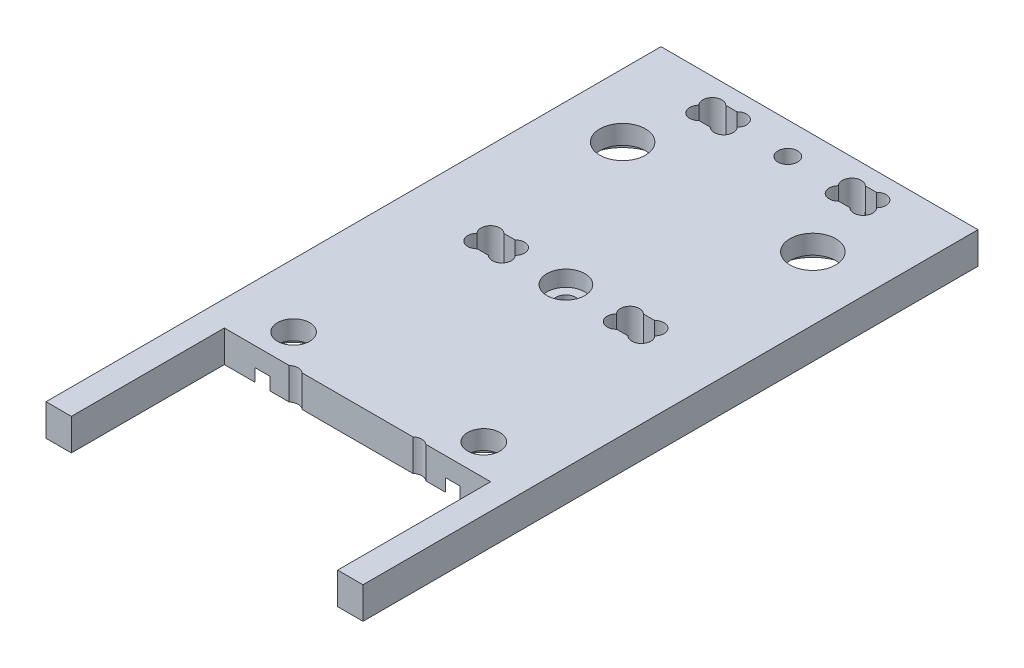
SolidWorks part; units mm, degrees
ref_plane "Alzado" through (0, 0, 0) normal (0, 0, 1) x (1, 0, 0)
ref_plane "Planta" through (0, 0, 0) normal (0, 1, 0) x (1, 0, 0)
ref_plane "Vista lateral" through (0, 0, 0) normal (1, 0, 0) x (0, 0, -1)
sketch "Croquis1" plane through (0, 0, 0) normal (0, 1, 0) x (1, 0, 0)
  line L0 (0, -36.0891) -> (0, 0) construction
  line L1 (-25, -48.5) -> (25, -48.5)
  line L2 (-25, -48.5) -> (-25, 48.5)
  line L3 (-25, 48.5) -> (25, 48.5)
  line L4 (25, -48.5) -> (25, 48.5)
  line L5 (-25, -48.5) -> (25, 48.5) construction
  line L6 (-25, 48.5) -> (25, -48.5) construction
  point P0 (0, 0)
  dimension "D2" = 50
  dimension "D1" = 97
extrude "Saliente-Extruir1" add sketch "Croquis1" along normal blind 5
sketch "Croquis3" plane through (0, 5, 0) normal (0, 1, 0) x (1, 0, 0)
  line L0 (0, -48.5) -> (0, 48.5) construction
  line L1 (-25, -48.5) -> (25, -48.5) construction
  line L2 (-14.1, -41.5) -> (-14.1, -48.5)
  line L3 (25, -48.5) -> (14.1, -48.5)
  line L4 (-25, -28.05) -> (-25, -48.5)
  line L5 (25, -28.05) -> (25, -48.5)
  line L6 (-25, -48.5) -> (-14.1, -48.5)
  line L7 (14.1, -41.5) -> (14.1, -48.5)
  line L10 (25, 48.5) -> (-25, 48.5) construction
  arc A0 (14.1, -41.5) -> (25, -28.05) centre (28.8286, -42.2945) cw
  arc A1 (-14.1, -41.5) -> (-25, -28.05) centre (-28.8286, -42.2945) ccw
  dimension "D1" = 7
  dimension "D3" = 29.5
  dimension "D2" = 20.45
  dimension "D4" = 14.1
extrude "Cortar-Extruir1" [suppressed] cut sketch "Croquis3" against normal through all
sketch "Croquis2" plane through (0, 5, 0) normal (0, 1, 0) x (1, 0, 0)
  line L0 (0, 6.5) -> (0, 48.5) construction
  line L1 (-15, -19.45) -> (15, -19.45) construction
  line L2 (-15, -19.45) -> (-15, 32.45) construction
  line L3 (-15, 32.45) -> (15, 32.45) construction
  line L4 (15, -19.45) -> (15, 32.45) construction
  line L5 (-15, -19.45) -> (15, 32.45) construction
  line L6 (-15, 32.45) -> (15, -19.45) construction
  line L7 (25, 48.5) -> (-25, 48.5) construction
  circle A0 centre (-15, 32.45) radius 3.6
  circle A1 centre (15, 32.45) radius 3.6
  circle A2 centre (15, -19.45) radius 2.55
  circle A3 centre (-15, -19.45) radius 2.55
  point P0 (0, 6.5)
  dimension "D3" = 7.2
  dimension "D5" = 5.1
  dimension "D1" = 30
  dimension "D2" = 51.9
  dimension "D4" = 42
extrude "Cortar-Extruir2" cut sketch "Croquis2" against normal through all
sketch "Croquis4" plane through (0, 0, 0) normal (0, -1, 0) x (1, 0, 0)
  circle A0 centre (15, -32.45) radius 6
  circle A1 centre (-15, -32.45) radius 6
  circle A2 centre (-15, 19.45) radius 5.05
  circle A3 centre (15, 19.45) radius 5.05
  dimension "D1" = 12
  dimension "D2" = 10.1
extrude "Cortar-Extruir3" cut sketch "Croquis4" against normal blind 2
fillet "Redondeo1" [suppressed] radius 5
sketch "Croquis5" plane through (0, 5, 0) normal (0, 1, 0) x (1, 0, 0)
  line L1 (-25, 45.6) -> (25, 45.6) construction
  line L2 (-25, 45.6) -> (-25, 41.4) construction
  line L3 (-25, 41.4) -> (25, 41.4) construction
  line L4 (25, 45.6) -> (25, 41.4) construction
  line L5 (-25, 48.5) -> (-25, -48.5) construction
  line L6 (25, -48.5) -> (25, 48.5) construction
  line L7 (25, 48.5) -> (-25, 48.5) construction
  line L8 (-11, 45.6) -> (-11, 41.4) construction
  line L9 (-14, 45.6) -> (-8, 45.6)
  line L10 (-14, 45.6) -> (-14, 41.4)
  line L11 (-14, 41.4) -> (-8, 41.4)
  line L12 (-8, 45.6) -> (-8, 41.4)
  line L13 (8, 45.6) -> (14, 45.6)
  line L14 (8, 45.6) -> (8, 41.4)
  line L15 (8, 41.4) -> (14, 41.4)
  line L16 (14, 45.6) -> (14, 41.4)
  line L17 (11, 45.6) -> (11, 41.4) construction
  line L18 (-11, 43.5) -> (-25, 43.5) construction
  line L19 (11, 43.5) -> (25, 43.5) construction
  line L20 (0, 45.6) -> (0, 41.4) construction
  circle A0 centre (0, 43.5) radius 1.55
  dimension "D5" = 3.1
  dimension "D1" = 4.2
  dimension "D2" = 2.9
  dimension "D3" = 6
  dimension "D4" = 14
extrude "Cortar-Extruir4" cut sketch "Croquis5" against normal through all
ref_plane "Plano1" through (0, 0, -43.5) normal (0, 0, 1) x (1, 0, 0)
ref_plane "Plano2" through (0, 0, -8.5) normal (0, 0, -1) x (-1, 0, 0)
ref_plane "Plano3" through (0, 0, -26) normal (0, 0, 1) x (1, 0, 0)
ref_plane "Plano5" through (0, 2.5, 0) normal (0, -1, 0) x (-1, 0, 0)
sketch "Croquis8" plane through (0, 5, 0) normal (0, 1, 0) x (1, 0, 0)
  line L0 (0, 43.5) -> (0, 51.5203) construction
  line L1 (-11.8787, 45.6) -> (-10.1213, 45.6)
  line L2 (-8, 45.6) -> (-14, 45.6) construction
  line L3 (-10.1213, 41.4) -> (-11.8787, 41.4)
  line L4 (-14, 45.6) -> (-14, 41.4) construction
  line L5 (-14, 45.6) -> (-12.5, 44.1) construction
  line L6 (-14, 41.4) -> (-8, 41.4) construction
  line L7 (14, 45.6) -> (12.5, 44.1) construction
  line L8 (10.1213, 41.4) -> (11.8787, 41.4)
  line L9 (11.8787, 45.6) -> (10.1213, 45.6)
  arc A0 (-11.8787, 45.6) -> (-14.0209, 43.5) centre (-12.9393, 44.5393) ccw
  arc A1 (-7.9791, 43.5) -> (-10.1213, 45.6) centre (-9.0607, 44.5393) ccw
  arc A2 (-10.1213, 41.4) -> (-7.9791, 43.5) centre (-9.0607, 42.4607) ccw
  arc A3 (-14.0209, 43.5) -> (-11.8787, 41.4) centre (-12.9393, 42.4607) ccw
  circle A4 centre (-12.5, 44.1) radius 1.5 construction
  circle A5 centre (12.5, 44.1) radius 1.5 construction
  arc A6 (14.0209, 43.5) -> (11.8787, 41.4) centre (12.9393, 42.4607) cw
  arc A7 (10.1213, 41.4) -> (7.9791, 43.5) centre (9.0607, 42.4607) cw
  arc A8 (7.9791, 43.5) -> (10.1213, 45.6) centre (9.0607, 44.5393) cw
  arc A9 (11.8787, 45.6) -> (14.0209, 43.5) centre (12.9393, 44.5393) cw
  dimension "D1" = 3
extrude "Cortar-Extruir6" cut sketch "Croquis8" against normal through all
mirror "Simetría1" about plane through (0, 0, -26) normal (0, 0, 1) of "Cortar-Extruir6", "Cortar-Extruir4"
sketch "Croquis14" plane through (0, 5, 0) normal (0, 1, 0) x (1, 0, 0)
  circle A0 centre (0, 8.5) radius 3
  dimension "D1" = 6
extrude "Cortar-Extruir9" cut sketch "Croquis14" against normal blind 2.5
sketch "Croquis17" plane through (0, 0, 0) normal (0, 1, 0) x (1, 0, 0)
  line L1 (-40, -60) -> (40, -60)
  line L2 (-40, -60) -> (-40, 60)
  line L3 (-40, 60) -> (40, 60)
  line L4 (40, -60) -> (40, 60)
  point P0 (0, 0)
  dimension "D1" = 120
  dimension "D2" = 80
sketch "Croquis18" plane through (0, 5, 0) normal (0, 1, 0) x (1, 0, 0)
  line L0 (-25, -48.5) -> (25, -48.5) construction
  line L1 (0, -35.5) -> (0, -48.5) construction
  line L3 (9.75, -45.5) -> (-9.75, -45.5) construction
  line L4 (9.75, -45.5) -> (9.75, -25.5) construction
  line L5 (9.75, -25.5) -> (-9.75, -25.5) construction
  line L6 (-9.75, -45.5) -> (-9.75, -25.5) construction
  line L7 (9.75, -45.5) -> (-9.75, -25.5) construction
  line L8 (9.75, -25.5) -> (-9.75, -45.5) construction
  circle A0 centre (0, -35.5) radius 10.5
  circle A2 centre (9.75, -45.5) radius 1.525
  circle A3 centre (-9.75, -45.5) radius 1.525
  circle A4 centre (9.75, -25.5) radius 1.525
  circle A5 centre (-9.75, -25.5) radius 1.525
  dimension "D2" = 21
  dimension "D5" = 3.05
  dimension "D1" = 13
  dimension "D3" = 20
  dimension "D4" = 19.5
extrude "Cortar-Extruir10" cut sketch "Croquis18" against normal through all
sketch "Croquis20" plane through (0, 0, 0) normal (0, -1, 0) x (1, 0, 0)
  line L0 (-21, 50.3214) -> (-21, 24.3653)
  line L1 (-21, 24.3653) -> (21, 24.3653)
  line L2 (21, 24.3653) -> (21, 50.3214)
  line L3 (21, 50.3214) -> (-21, 50.3214)
  line L4 (-25, -48.5) -> (-25, 48.5) construction
  line L5 (25, 48.5) -> (25, -48.5) construction
  dimension "D1" = 4
  dimension "D2" = 4
extrude "Cortar-Extruir11" cut sketch "Croquis20" against normal through all
